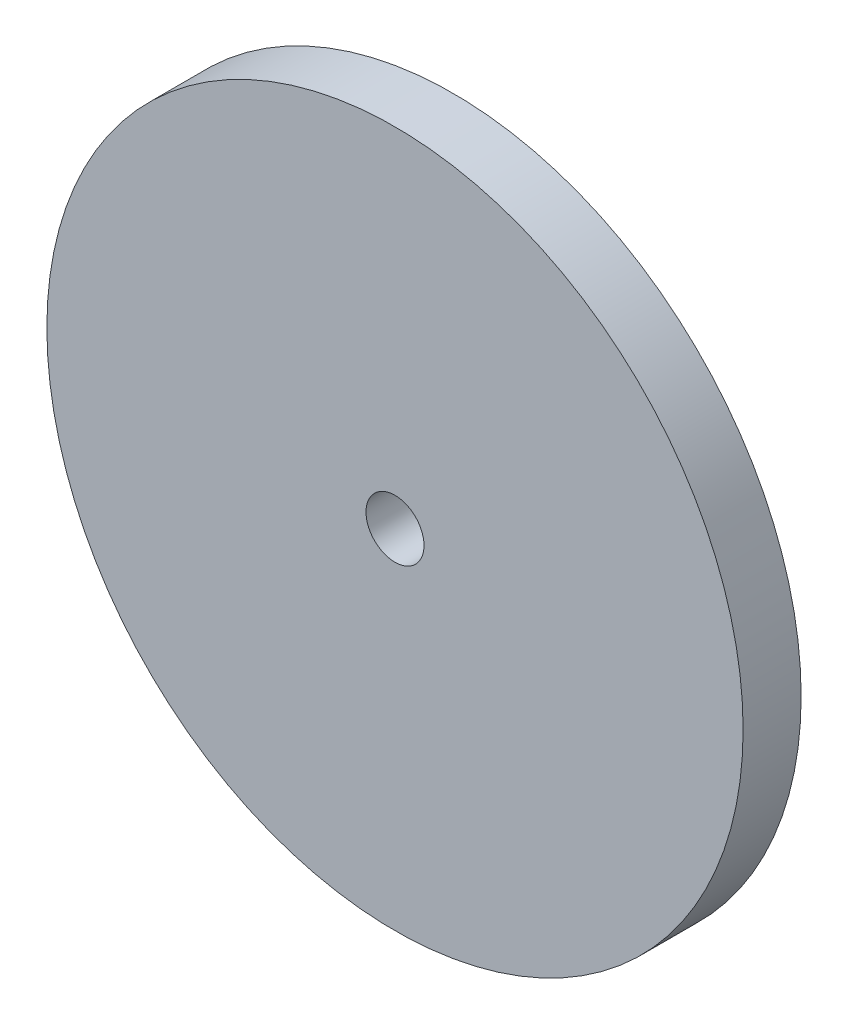
SolidWorks part; units mm, degrees
ref_plane "Front Plane" through (0, 0, 0) normal (0, 0, 1) x (1, 0, 0)
ref_plane "Top Plane" through (0, 0, 0) normal (0, 1, 0) x (1, 0, 0)
ref_plane "Right Plane" through (0, 0, 0) normal (1, 0, 0) x (0, 0, -1)
sketch "Sketch1" plane through (0, 0, 0) normal (0, 0, 1) x (1, 0, 0)
  circle A0 centre (0, 0) radius 30
  dimension "D1" = 60
extrude "Boss-Extrude1" add sketch "Sketch1" along normal blind 5
sketch "Sketch2" plane through (0, 0, 5) normal (0, 0, 1) x (1, 0, 0)
  circle A0 centre (0, 0) radius 2.5
  dimension "D1" = 5
extrude "Cut-Extrude1" cut sketch "Sketch2" against normal blind 5
